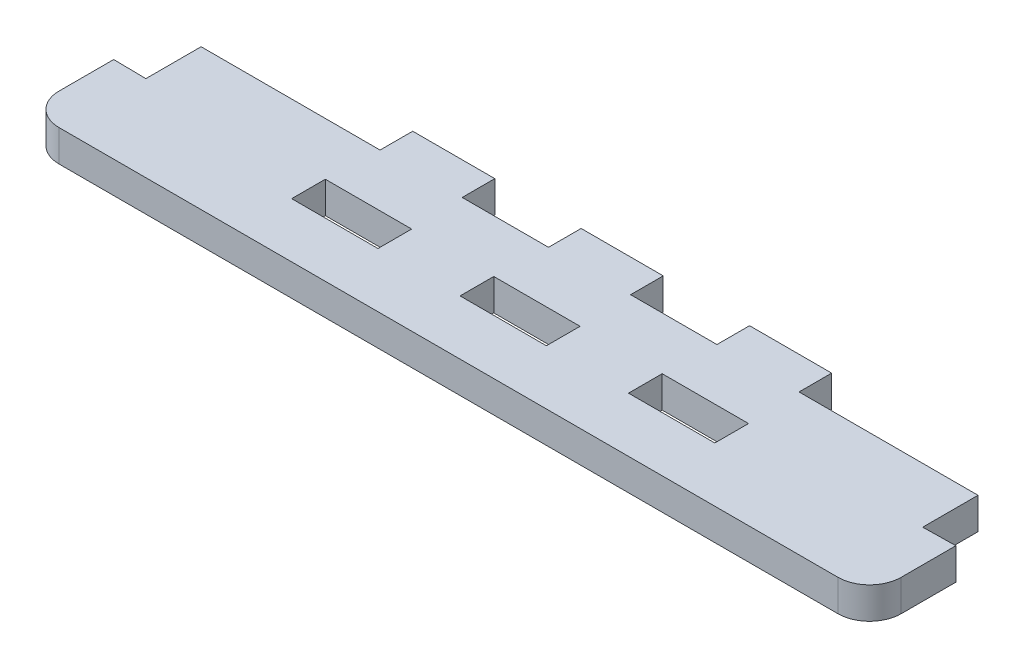
SolidWorks part; units mm, degrees
ref_plane "Front Plane" through (0, 0, 0) normal (0, 0, 1) x (1, 0, 0)
ref_plane "Top Plane" through (0, 0, 0) normal (0, 1, 0) x (1, 0, 0)
ref_plane "Right Plane" through (0, 0, 0) normal (1, 0, 0) x (0, 0, -1)
sketch "Sketch1" plane through (0, 0, 0) normal (0, 1, 0) x (1, 0, 0)
  line L1 (0, 0) -> (80, 0)
  line L2 (0, 0) -> (0, -16.5)
  line L3 (0, -16.5) -> (80, -16.5)
  line L4 (80, 0) -> (80, -16.5)
sketch "Sketch2" plane through (0, 0, 0) normal (1, 0, 0) x (0, 0, -1)
  line L1 (0, 0) -> (-16.5, 0)
  line L2 (0, 0) -> (0, -3)
  line L3 (0, -3) -> (-16.5, -3)
  line L4 (-16.5, 0) -> (-16.5, -3)
extrude "Boss-Extrude1" add sketch "Sketch1" against normal up to vertex (3 mm away) up to point (0, -3, 0)
sketch "Sketch3" plane through (0, 0, 0) normal (0, 1, 0) x (1, 0, 0)
  line L4 (20, -8.2) -> (20, -11.2)
  line L5 (20, -11.2) -> (28, -11.2)
  line L6 (28, -11.2) -> (28, -8.2)
  line L7 (28, -8.2) -> (20, -8.2)
  line L8 (20, -8.2) -> (20, -11.2) construction
  line L9 (20, -11.2) -> (28, -11.2) construction
  line L10 (28, -11.2) -> (28, -8.2) construction
  line L11 (28, -8.2) -> (20, -8.2) construction
  line L12 (36, -8.2) -> (36, -11.2)
  line L13 (36, -11.2) -> (44, -11.2)
  line L14 (44, -11.2) -> (44, -8.2)
  line L15 (44, -8.2) -> (36, -8.2)
  line L16 (36, -8.2) -> (36, -11.2) construction
  line L17 (36, -11.2) -> (44, -11.2) construction
  line L18 (44, -11.2) -> (44, -8.2) construction
  line L19 (44, -8.2) -> (36, -8.2) construction
  line L20 (28, 0) -> (28, -3)
  line L21 (28, -3) -> (36, -3)
  line L22 (36, -3) -> (36, 0)
  line L23 (36, 0) -> (28, 0)
  line L24 (28, 0) -> (28, -3) construction
  line L25 (28, -3) -> (36, -3) construction
  line L26 (36, -3) -> (36, 0) construction
  line L27 (36, 0) -> (28, 0) construction
  line L28 (60, -11.2) -> (60, -8.2)
  line L29 (60, -8.2) -> (52, -8.2)
  line L30 (52, -8.2) -> (52, -11.2)
  line L31 (52, -11.2) -> (60, -11.2)
  line L32 (60, -11.2) -> (60, -8.2) construction
  line L33 (60, -8.2) -> (52, -8.2) construction
  line L34 (52, -8.2) -> (52, -11.2) construction
  line L35 (52, -11.2) -> (60, -11.2) construction
  line L36 (44, 0) -> (44, -3)
  line L37 (44, -3) -> (52, -3)
  line L38 (52, -3) -> (52, 0)
  line L39 (52, 0) -> (44, 0)
  line L40 (44, 0) -> (44, -3) construction
  line L41 (44, -3) -> (52, -3) construction
  line L42 (52, -3) -> (52, 0) construction
  line L43 (52, 0) -> (44, 0) construction
  line L46 (77, -3) -> (77, -8.25)
  line L47 (77, -8.25) -> (80, -8.2)
  line L48 (80, -8.2) -> (80, 0)
  line L49 (80, 0) -> (60, 0)
  line L50 (60, 0) -> (60, -3)
  line L51 (60, -3) -> (77, -3)
  line L52 (77, -3) -> (77, -8.25) construction
  line L53 (77, -8.25) -> (80, -8.2) construction
  line L54 (80, -8.2) -> (80, 0) construction
  line L55 (80, 0) -> (60, 0) construction
  line L56 (60, 0) -> (60, -3) construction
  line L57 (60, -3) -> (77, -3) construction
  line L58 (0, -8.2) -> (3, -8.25)
  line L59 (3, -8.25) -> (3, -3)
  line L60 (3, -3) -> (20, -3)
  line L61 (20, -3) -> (20, 0)
  line L62 (20, 0) -> (0, 0)
  line L63 (0, 0) -> (0, -8.2)
  line L64 (0, -8.2) -> (3, -8.25) construction
  line L65 (3, -8.25) -> (3, -3) construction
  line L66 (3, -3) -> (20, -3) construction
  line L67 (20, -3) -> (20, 0) construction
  line L68 (20, 0) -> (0, 0) construction
  line L69 (0, 0) -> (0, -8.2) construction
  line L96 (19.9, -8.1) -> (19.9, -11.3)
  line L97 (19.9, -11.3) -> (28.1, -11.3)
  line L98 (28.1, -11.3) -> (28.1, -8.1)
  line L99 (28.1, -8.1) -> (19.9, -8.1)
  line L100 (35.9, -8.1) -> (35.9, -11.3)
  line L101 (35.9, -11.3) -> (44.1, -11.3)
  line L102 (44.1, -11.3) -> (44.1, -8.1)
  line L103 (44.1, -8.1) -> (35.9, -8.1)
  line L104 (27.9, 0.1) -> (27.9, -3.1)
  line L105 (27.9, -3.1) -> (36.1, -3.1)
  line L106 (36.1, -3.1) -> (36.1, 0.1)
  line L107 (36.1, 0.1) -> (27.9, 0.1)
  line L108 (60.1, -11.3) -> (60.1, -8.1)
  line L109 (60.1, -8.1) -> (51.9, -8.1)
  line L110 (51.9, -8.1) -> (51.9, -11.3)
  line L111 (51.9, -11.3) -> (60.1, -11.3)
  line L112 (43.9, 0.1) -> (43.9, -3.1)
  line L113 (43.9, -3.1) -> (52.1, -3.1)
  line L114 (52.1, -3.1) -> (52.1, 0.1)
  line L115 (52.1, 0.1) -> (43.9, 0.1)
  line L116 (76.9, -3.1) -> (76.9, -8.3517)
  line L117 (76.9, -8.3517) -> (80.1, -8.2983)
  line L118 (80.1, -8.2983) -> (80.1, 0.1)
  line L119 (80.1, 0.1) -> (59.9, 0.1)
  line L120 (59.9, 0.1) -> (59.9, -3.1)
  line L121 (59.9, -3.1) -> (76.9, -3.1)
  line L122 (-0.1, -8.2983) -> (3.1, -8.3517)
  line L123 (3.1, -8.3517) -> (3.1, -3.1)
  line L124 (3.1, -3.1) -> (20.1, -3.1)
  line L125 (20.1, -3.1) -> (20.1, 0.1)
  line L126 (20.1, 0.1) -> (-0.1, 0.1)
  line L127 (-0.1, 0.1) -> (-0.1, -8.2983)
  dimension "D1" = 0
  dimension "D2" = 0
  dimension "D3" = 0
  dimension "D4" = 0
  dimension "D5" = 0
  dimension "D6" = 0
  dimension "D7" = 0
  dimension "D8" = 0.1
extrude "Cut-Extrude1" cut sketch "Sketch3" against normal through all
fillet "Fillet1" radius 3 2 edges at (80, -1.5, 16.5) (0, -1.5, 16.5)
